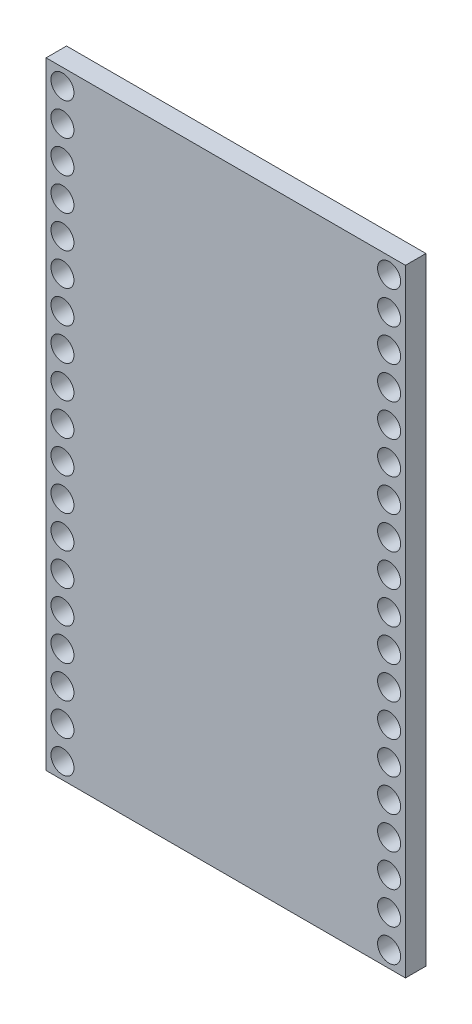
SolidWorks part; units mm, degrees
ref_plane "Front Plane" through (0, 0, 0) normal (0, 0, 1) x (1, 0, 0)
ref_plane "Top Plane" through (0, 0, 0) normal (0, 1, 0) x (1, 0, 0)
ref_plane "Right Plane" through (0, 0, 0) normal (1, 0, 0) x (0, 0, -1)
sketch "Эскиз-Плата" plane through (0, 0, 0) normal (0, 0, 1) x (1, 0, 0)
  line L0 (0, 24.13) -> (0, -24.13) construction
  line L1 (-14.05, -24.13) -> (14.05, -24.13)
  line L2 (-14.05, -24.13) -> (-14.05, 24.13)
  line L3 (-14.05, 24.13) -> (14.05, 24.13)
  line L4 (14.05, -24.13) -> (14.05, 24.13)
  line L5 (-14.05, -24.13) -> (14.05, 24.13) construction
  line L6 (-14.05, 24.13) -> (14.05, -24.13) construction
  line L7 (-12.77, 22.85) -> (-12.77, 20.31) construction
  line L8 (-12.77, 24.13) -> (-12.77, -24.13) construction
  line L9 (12.77, 24.13) -> (12.77, -24.13) construction
  line L10 (-14.05, 22.85) -> (14.05, 22.85) construction
  line L11 (-14.05, -22.87) -> (14.05, -22.87) construction
  circle A0 centre (-12.77, 22.85) radius 0.9
  circle A1 centre (12.77, 22.85) radius 0.9
  circle A2 centre (-12.77, 20.31) radius 0.9
  circle A3 centre (12.77, 20.31) radius 0.9
  circle A4 centre (-12.77, 17.77) radius 0.9
  circle A5 centre (12.77, 17.77) radius 0.9
  circle A6 centre (-12.77, 15.23) radius 0.9
  circle A7 centre (12.77, 15.23) radius 0.9
  circle A8 centre (-12.77, 12.69) radius 0.9
  circle A9 centre (12.77, 12.69) radius 0.9
  circle A10 centre (-12.77, 10.15) radius 0.9
  circle A11 centre (12.77, 10.15) radius 0.9
  circle A12 centre (-12.77, 7.61) radius 0.9
  circle A13 centre (12.77, 7.61) radius 0.9
  circle A14 centre (-12.77, 5.07) radius 0.9
  circle A15 centre (12.77, 5.07) radius 0.9
  circle A16 centre (-12.77, 2.53) radius 0.9
  circle A17 centre (12.77, 2.53) radius 0.9
  circle A18 centre (-12.77, -0.01) radius 0.9
  circle A19 centre (12.77, -0.01) radius 0.9
  circle A20 centre (-12.77, -2.55) radius 0.9
  circle A21 centre (12.77, -2.55) radius 0.9
  circle A22 centre (-12.77, -5.09) radius 0.9
  circle A23 centre (12.77, -5.09) radius 0.9
  circle A24 centre (-12.77, -7.63) radius 0.9
  circle A25 centre (12.77, -7.63) radius 0.9
  circle A26 centre (-12.77, -10.17) radius 0.9
  circle A27 centre (12.77, -10.17) radius 0.9
  circle A28 centre (-12.77, -12.71) radius 0.9
  circle A29 centre (12.77, -12.71) radius 0.9
  circle A30 centre (-12.77, -15.25) radius 0.9
  circle A31 centre (12.77, -15.25) radius 0.9
  circle A32 centre (-12.77, -17.79) radius 0.9
  circle A33 centre (12.77, -17.79) radius 0.9
  circle A34 centre (-12.77, -20.33) radius 0.9
  circle A35 centre (12.77, -20.33) radius 0.9
  circle A36 centre (-12.77, -22.87) radius 0.9
  circle A37 centre (12.77, -22.87) radius 0.9
  point P0 (0, 0)
  dimension "D3" = 1.8
  dimension "D4" = 0.38
  dimension "D5" = 0.38
  dimension "D1" = 48.26
  dimension "D2" = 28.1
  dimension "D7" = 2.54
  dimension "D6" = 19
extrude "Бобышка-Плата" add sketch "Эскиз-Плата" along normal blind 1.6
ref_plane "Плоскость-Симметри" through (0, 0, 0) normal (1, 0, 0) x (0, 0, -1)
